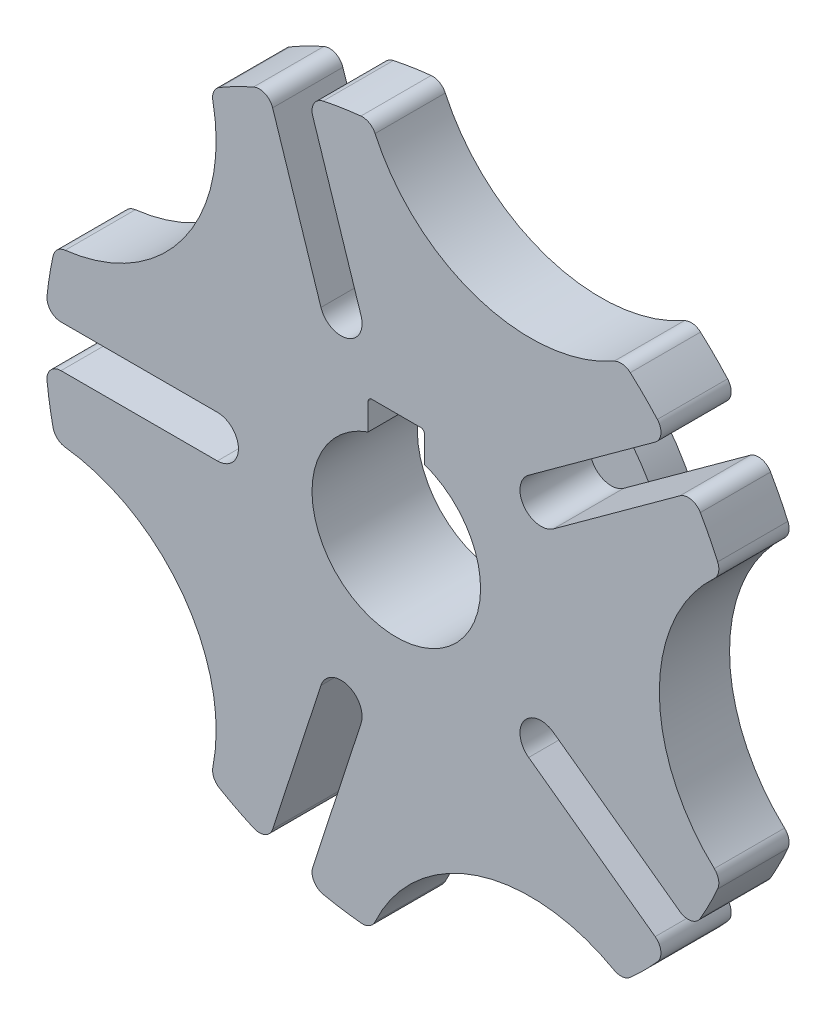
SolidWorks part; units mm, degrees
material "7075-O (SS)"
ref_plane "Front Plane" through (0, 0, 0) normal (0, 0, 1) x (1, 0, 0)
ref_plane "Top Plane" through (0, 0, 0) normal (0, 1, 0) x (1, 0, 0)
ref_plane "Right Plane" through (0, 0, 0) normal (1, 0, 0) x (0, 0, -1)
sketch "Sketch1" plane through (0, 0, 0) normal (0, 0, 1) x (1, 0, 0)
  line L0 (0, 0) -> (20.2254, 14.6946) construction
  line L1 (21.1071, 13.4811) -> (30.9017, 0) construction
  line L2 (30.9017, 0) -> (0, 0) construction
  line L3 (9.4237, 8.7008) -> (19.3437, 15.9082)
  line L4 (11.187, 6.2738) -> (21.1071, 13.4811)
  line L5 (18.7254, 14.6946) -> (18.7254, 0) construction
  line L6 (11.187, -6.2738) -> (21.1071, -13.4811)
  line L7 (9.4237, -8.7008) -> (19.3437, -15.9082)
  line L8 (-2.5097, -12.5782) -> (-6.2988, -24.2399)
  line L9 (-5.3629, -11.6512) -> (-9.152, -23.3129)
  line L10 (-12.7381, -1.5) -> (-25, -1.5)
  line L11 (-12.7381, 1.5) -> (-25, 1.5)
  line L12 (-5.3629, 11.6512) -> (-9.152, 23.3129)
  line L13 (-2.5097, 12.5782) -> (-6.2988, 24.2399)
  arc A0 (23.1646, 9.4021) -> (21.0703, 13.4552) centre (0, 0) ccw
  circle A1 centre (0, 0) radius 12.7381 construction
  circle A2 centre (30.9017, 0) radius 18.1636 construction
  arc A3 (9.4237, 8.7008) -> (11.187, 6.2738) centre (10.3054, 7.4873) ccw
  arc A5 (23.1646, 9.4021) -> (23.1646, -9.4021) centre (30.9017, 0) ccw
  arc A6 (21.0703, 13.4552) -> (19.3077, 15.8812) centre (20.2254, 14.6946) ccw
  arc A7 (19.3077, 15.8812) -> (23.1646, -9.4021) centre (0, 0) ccw
  arc A8 (16.1002, -19.1255) -> (-1.7837, -24.9363) centre (9.5492, -29.3893) ccw
  arc A9 (11.187, -6.2738) -> (9.4237, -8.7008) centre (10.3054, -7.4873) ccw
  arc A10 (19.3077, -15.8812) -> (21.0703, -13.4552) centre (20.2254, -14.6946) ccw
  arc A11 (-13.2142, -21.2223) -> (-24.267, -6.0094) centre (-25, -18.1636) ccw
  arc A12 (-2.5097, -12.5782) -> (-5.3629, -11.6512) centre (-3.9363, -12.1147) ccw
  arc A13 (-9.1375, -23.2703) -> (-6.2856, -24.1969) centre (-7.7254, -23.7764) ccw
  arc A14 (-24.267, 6.0094) -> (-13.2142, 21.2223) centre (-25, 18.1636) ccw
  arc A15 (-12.7381, -1.5) -> (-12.7381, 1.5) centre (-12.7381, 0) ccw
  arc A16 (-24.955, 1.4993) -> (-24.955, -1.4993) centre (-25, 0) ccw
  arc A17 (-1.7837, 24.9363) -> (16.1002, 19.1255) centre (9.5492, 29.3893) ccw
  arc A18 (-5.3629, 11.6512) -> (-2.5097, 12.5782) centre (-3.9363, 12.1147) ccw
  arc A19 (-6.2856, 24.1969) -> (-9.1375, 23.2703) centre (-7.7254, 23.7764) ccw
  point P64 (0, 0)
  dimension "D1" = 50
  dimension "D3" = 3
  dimension "D2" = 36
  dimension "D4" = 5
extrude "Boss-Extrude1" add sketch "Sketch1" along normal blind 5 contours A18 L12 A7 A14 L11 A15 L10 A11 L9 A12 L8 A8 L7 A9 L6 A5 A0 L4 A3 L3 A17 L13
sketch "Sketch2" plane through (0, 0, 0) normal (0, 0, 1) x (1, 0, 0)
  circle A0 centre (0, 0) radius 15
  dimension "D1" = 30
extrude "Boss-Extrude2" add sketch "Sketch2" against normal blind 2.5
sketch "Sketch3" plane through (0, 0, 0) normal (0, 0, 1) x (1, 0, 0)
  line L5 (-2, 7.8) -> (2, 7.8)
  line L6 (-2, 7.8) -> (-2, 4.2)
  line L7 (-2, 4.2) -> (2, 4.2)
  line L8 (2, 7.8) -> (2, 4.2)
  line L9 (-2, 7.8) -> (2, 4.2) construction
  line L10 (-2, 4.2) -> (2, 7.8) construction
  circle A0 centre (0, 0) radius 6
  point P0 (0, 0)
  point P1 (0, 6)
  dimension "D1" = 12
  dimension "D2" = 4
  dimension "D3" = 3.6
extrude "Cut-Extrude1" cut sketch "Sketch3" against normal through all both and the other way through all contours L6 A0 L8 L7
fillet "Fillet2" radius 0.25 2 edges at (2, 7.8, 1.25) (-2, 7.8, 1.25)
fillet "Fillet1" radius 1 20 edges at (-1.7837, 24.9363, 2.5) (16.1002, 19.1255, 2.5) (21.0707, 13.4546, 2.5) (19.3073, 15.8817, 2.5) (23.1646, 9.4021, 2.5) (23.1646, -9.4021, 2.5) (21.0707, -13.4546, 2.5) (19.3073, -15.8817, 2.5) (16.1002, -19.1255, 2.5) (-1.7837, -24.9363, 2.5) (-6.2849, -24.1971, 2.5) (-9.1381, -23.2701, 2.5) (-13.2142, -21.2223, 2.5) (-24.267, -6.0094, 2.5) (-24.955, -1.5, 2.5) (-24.955, 1.5, 2.5) (-24.267, 6.0094, 2.5) (-13.2142, 21.2223, 2.5) (-9.1381, 23.2701, 2.5) (-6.2849, 24.1971, 2.5)
